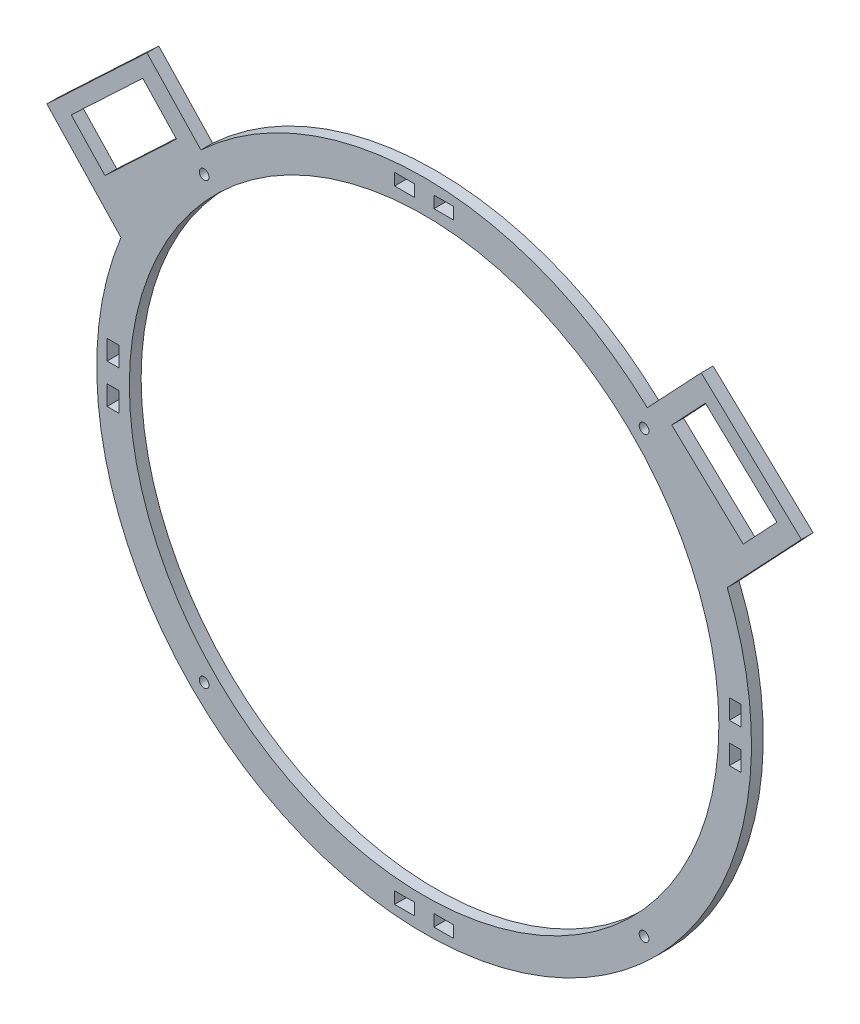
SolidWorks part; units mm, degrees
ref_plane "Alzado" through (0, 0, 0) normal (0, 0, 1) x (1, 0, 0)
ref_plane "Planta" through (0, 0, 0) normal (0, 1, 0) x (1, 0, 0)
ref_plane "Vista lateral" through (0, 0, 0) normal (1, 0, 0) x (0, 0, -1)
sketch "Croquis1" plane through (0, 0, 0) normal (0, 0, 1) x (1, 0, 0)
  line L0 (-44.7644, 42.1119) -> (355.2356, 42.1119)
  line L1 (355.2356, 42.1119) -> (355.2356, -357.8881)
  line L2 (355.2356, -357.8881) -> (-44.7644, -357.8881)
  line L3 (-44.7644, -357.8881) -> (-44.7644, 42.1119)
  line L4 (51.705, -49.341) -> (50.9394, -50.0625)
  line L5 (40.601, -36.9999) -> (13.1692, -7.8881)
  line L6 (13.1692, -7.8881) -> (-37.7765, -55.8938)
  line L7 (-37.7765, -55.8938) -> (-0.0578, -95.9225)
  line L8 (13.1692, -7.8881) -> (5.8912, -14.7461)
  line L10 (11.0347, -20.2045) -> (-25.3551, -54.4943)
  line L11 (-25.3551, -54.4943) -> (-8.2102, -72.6891)
  line L12 (-8.2102, -72.6891) -> (28.1796, -38.3994)
  line L13 (28.1796, -38.3994) -> (11.0347, -20.2045)
  line L14 (280.202, -38.3994) -> (297.3469, -20.2045)
  line L15 (316.5918, -72.6891) -> (280.202, -38.3994)
  line L16 (333.7367, -54.4943) -> (316.5918, -72.6891)
  line L17 (297.3469, -20.2045) -> (333.7367, -54.4943)
  line L18 (295.2124, -7.8881) -> (302.4904, -14.7461)
  line L19 (346.1581, -55.8938) -> (308.4393, -95.9225)
  line L20 (295.2124, -7.8881) -> (346.1581, -55.8938)
  line L21 (267.7806, -36.9999) -> (295.2124, -7.8881)
  circle A0 centre (154.1908, -158.8703) radius 150
  arc A1 (-0.0578, -95.9225) -> (308.4393, -95.9225) centre (154.1908, -158.8703) ccw
  arc A2 (267.7806, -36.9999) -> (40.601, -36.9999) centre (154.1908, -158.8703) ccw
  dimension "D3" = 40
  dimension "D1" = 400
  dimension "D2" = 400
  dimension "D4" = 70
  dimension "D5" = 55
extrude "Saliente-Extruir1" add sketch "Croquis1" along normal blind 6 contours L21 A2 L5 L6 L7 A1 L19 L20 L18 L14 L17 L16 L15 L13 L12 L11 L10 A0
sketch "Croquis2" plane through (0, 0, 6) normal (0, 0, 1) x (1, 0, 0)
  line L0 (154.1908, -8.8703) -> (154.1908, 7.7281)
  line L1 (154.1908, -308.8703) -> (154.1908, -325.4688)
  line L2 (304.1908, -158.8703) -> (320.7893, -158.8703)
  line L3 (4.1908, -158.8703) -> (-12.4077, -158.8703)
  line L4 (36.3879, -276.6733) -> (48.1248, -264.9364)
  line L5 (271.9937, -276.6733) -> (260.2568, -264.9364)
  line L6 (48.1248, -52.8043) -> (36.3879, -41.0674)
  line L7 (260.2568, -52.8043) -> (271.9937, -41.0674)
  line L8 (159.1908, 2.4289) -> (169.1908, 2.4289)
  line L9 (149.1908, 2.4289) -> (139.1908, 2.4289)
  line L10 (149.1908, -0.5711) -> (149.1908, 2.4289)
  line L11 (149.1908, -0.5711) -> (149.1908, -3.5711)
  line L12 (149.1908, -3.5711) -> (159.1908, -3.5711)
  line L13 (159.1908, -3.5711) -> (159.1908, 2.4289)
  line L14 (159.1908, 2.4289) -> (149.1908, 2.4289)
  line L15 (139.1908, 2.4289) -> (139.1908, -3.5711)
  line L16 (139.1908, -3.5711) -> (169.1908, -3.5711)
  line L17 (169.1908, -3.5711) -> (169.1908, 2.4289)
  line L18 (169.1908, -314.1696) -> (169.1908, -320.1696)
  line L19 (139.1908, -314.1696) -> (169.1908, -314.1696)
  line L20 (139.1908, -320.1696) -> (139.1908, -314.1696)
  line L21 (159.1908, -320.1696) -> (149.1908, -320.1696)
  line L22 (159.1908, -314.1696) -> (159.1908, -320.1696)
  line L23 (149.1908, -314.1696) -> (159.1908, -314.1696)
  line L24 (149.1908, -317.1696) -> (149.1908, -314.1696)
  line L25 (149.1908, -317.1696) -> (149.1908, -320.1696)
  line L26 (149.1908, -320.1696) -> (139.1908, -320.1696)
  line L27 (159.1908, -320.1696) -> (169.1908, -320.1696)
  line L28 (-4.1084, -158.8703) -> (-4.1084, -153.8703)
  line L29 (-4.1084, -158.8703) -> (-4.1084, -163.8703)
  line L30 (-4.1084, -163.8703) -> (-1.1084, -163.8703)
  line L31 (-4.1084, -163.8703) -> (-7.1084, -163.8703)
  line L32 (-7.1084, -163.8703) -> (-7.1084, -153.8703)
  line L33 (-7.1084, -153.8703) -> (-1.1084, -153.8703)
  line L34 (-1.1084, -153.8703) -> (-1.1084, -163.8703)
  line L35 (-1.1084, -163.8703) -> (-1.1084, -173.8703)
  line L36 (-1.1084, -173.8703) -> (-7.1084, -173.8703)
  line L37 (-7.1084, -173.8703) -> (-7.1084, -163.8703)
  line L38 (-7.1084, -153.8703) -> (-7.1084, -143.8703)
  line L39 (-7.1084, -143.8703) -> (-1.1084, -143.8703)
  line L40 (-1.1084, -143.8703) -> (-1.1084, -153.8703)
  line L41 (309.49, -143.8703) -> (309.49, -153.8703)
  line L42 (315.49, -143.8703) -> (309.49, -143.8703)
  line L43 (315.49, -153.8703) -> (315.49, -143.8703)
  line L44 (315.49, -173.8703) -> (315.49, -163.8703)
  line L45 (309.49, -173.8703) -> (315.49, -173.8703)
  line L46 (309.49, -163.8703) -> (309.49, -173.8703)
  line L47 (309.49, -153.8703) -> (309.49, -163.8703)
  line L48 (315.49, -153.8703) -> (309.49, -153.8703)
  line L49 (315.49, -163.8703) -> (315.49, -153.8703)
  line L50 (312.49, -163.8703) -> (315.49, -163.8703)
  line L51 (312.49, -163.8703) -> (309.49, -163.8703)
  line L52 (312.49, -158.8703) -> (312.49, -163.8703)
  line L53 (312.49, -158.8703) -> (312.49, -153.8703)
  circle A0 centre (154.1908, -158.8703) radius 150
  circle A1 centre (154.1908, -158.8703) radius 166.5985
  circle A2 centre (42.2563, -46.9359) radius 2.475
  circle A3 centre (266.1253, -46.9359) radius 2.475
  circle A4 centre (266.1253, -270.8048) radius 2.475
  circle A5 centre (42.2563, -270.8048) radius 2.475
  dimension "D1" = 4.95
  dimension "D2" = 4.95
  dimension "D3" = 4.95
  dimension "D4" = 4.95
  dimension "D5" = 45
  dimension "D8" = 45
extrude "Cortar-Extruir1" cut sketch "Croquis2" against normal blind 10 contours L15 L16 L11 L10 L9 | L16 L17 L8 L13 | L48 L43 L42 L41 | L50 L51 L46 L45 L44 | L22 L27 L18 L19 | L26 L25 L24 L19 L20 | L40 L39 L38 L33 | L37 L36 L35 L30 L31 | L6 A2 | L6 A2 | L7 A3 | L7 A3 | L5 A4 | L5 A4 | L4 A5 | L4 A5
